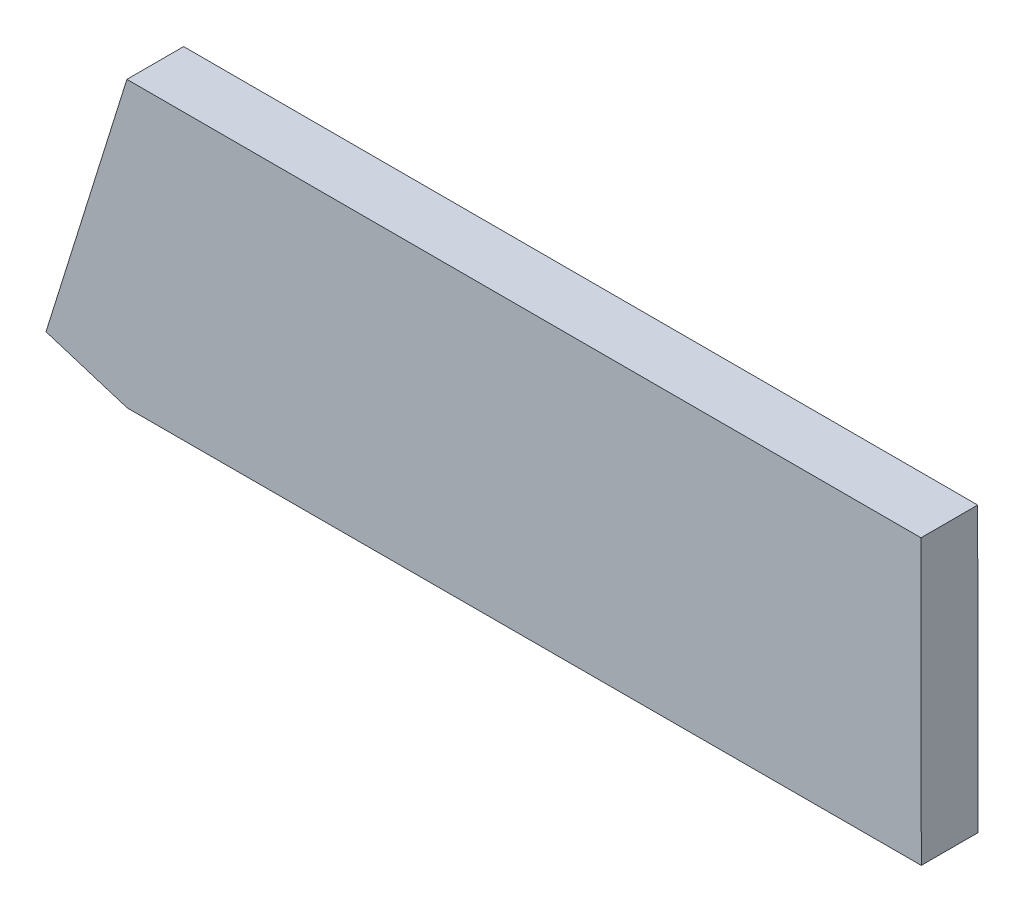
SolidWorks part; units mm, degrees
ref_plane "Front Plane" through (0, 0, 0) normal (0, 0, 1) x (1, 0, 0)
ref_plane "Top Plane" through (0, 0, 0) normal (0, 1, 0) x (1, 0, 0)
ref_plane "Right Plane" through (0, 0, 0) normal (1, 0, 0) x (0, 0, -1)
sketch "Sketch1" plane through (0, 0, 0) normal (0, 0, 1) x (1, 0, 0)
  line L0 (-44.45, 15.8984) -> (44.45, 15.8984)
  line L1 (-44.45, 15.8984) -> (-53.5084, -13.1057)
  line L2 (-44.4165, -15.9453) -> (44.4835, -15.8515)
  line L3 (44.45, 15.8984) -> (44.4835, -15.8515)
  line L7 (-53.5084, -13.1057) -> (-44.4165, -15.9453)
  dimension "D2" = 31.75
  dimension "D3" = 88.9
  dimension "D12" = 9.525
  dimension "D13" = 30.3858
  dimension "D15" = 88.9
extrude "Boss-Extrude1" add sketch "Sketch1" along normal blind 6.35 contours L0 L3 L2 L7 L1
